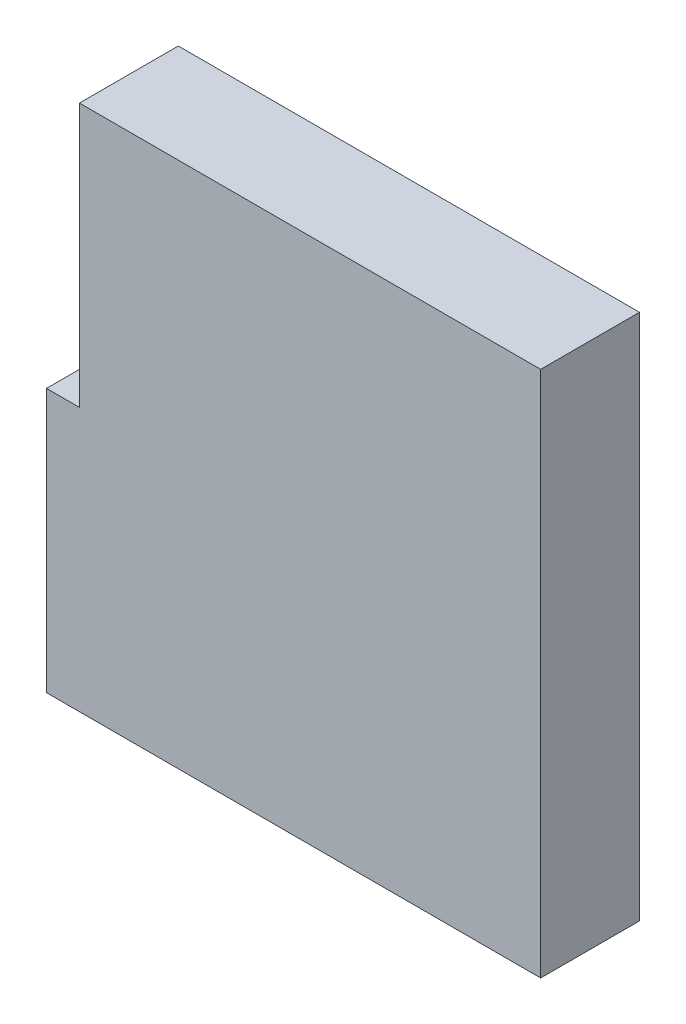
SolidWorks part; units mm, degrees
ref_plane "Front Plane" through (0, 0, 0) normal (0, 0, 1) x (1, 0, 0)
ref_plane "Top Plane" through (0, 0, 0) normal (0, 1, 0) x (1, 0, 0)
ref_plane "Right Plane" through (0, 0, 0) normal (1, 0, 0) x (0, 0, -1)
sketch "Sketch1" plane through (0, 0, 0) normal (0, 0, 1) x (1, 0, 0)
  line L0 (-190.5, 101.6) -> (-190.5, 0)
  line L1 (-190.5, 0) -> (0, 0)
  line L2 (0, 0) -> (0, 203.2)
  line L3 (0, 203.2) -> (-177.8, 203.2)
  line L4 (-177.8, 203.2) -> (-177.8, 101.6)
  line L5 (-177.8, 101.6) -> (-190.5, 101.6)
  dimension "D1" = 190.5
  dimension "D2" = 203.2
  dimension "D3" = 101.6
  dimension "D4" = 12.7
extrude "Boss-Extrude1" add sketch "Sketch1" along normal blind 38.1 contours L4 L5 L0 L1 L2 L3
